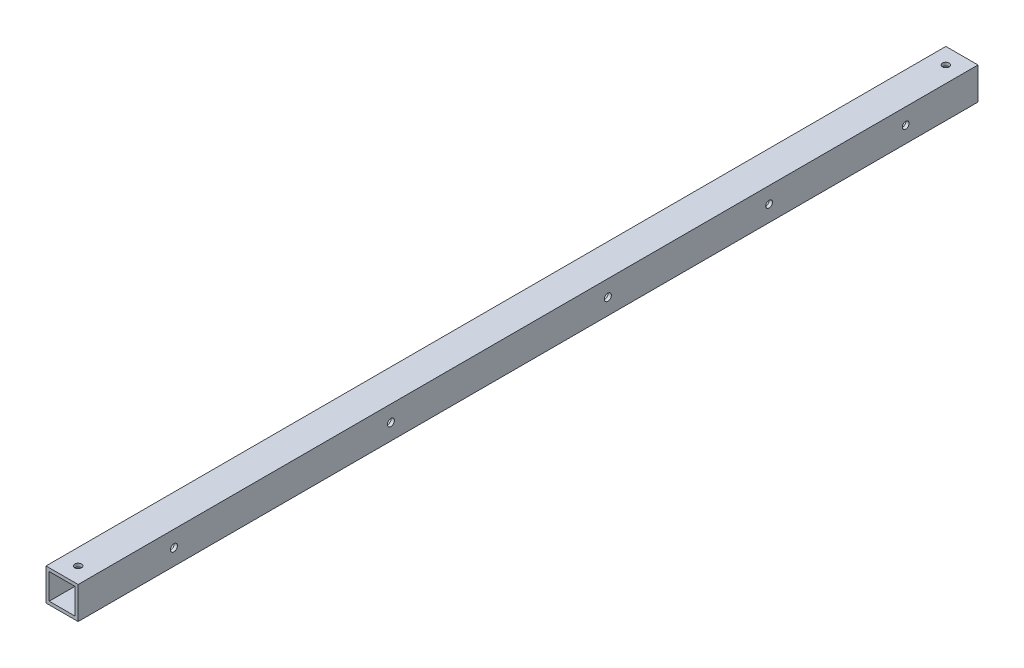
SolidWorks part; units mm, degrees
ref_plane "正面" through (0, 0, 0) normal (0, 0, 1) x (1, 0, 0)
ref_plane "平面" through (0, 0, 0) normal (0, 1, 0) x (1, 0, 0)
ref_plane "右側面" through (0, 0, 0) normal (1, 0, 0) x (0, 0, -1)
sketch "ｽｹｯﾁ1" plane through (0, 0, 0) normal (0, 0, 1) x (1, 0, 0)
  line L1 (-8, 8) -> (8, 8)
  line L2 (-8, 8) -> (-8, -8)
  line L3 (-8, -8) -> (8, -8)
  line L4 (8, 8) -> (8, -8)
  line L5 (-8, 8) -> (8, -8) construction
  line L6 (-8, -8) -> (8, 8) construction
  line L7 (-10, 10) -> (10, 10)
  line L8 (-10, 10) -> (-10, -10)
  line L9 (-10, -10) -> (10, -10)
  line L10 (10, 10) -> (10, -10)
  line L11 (-10, 10) -> (10, -10) construction
  line L12 (-10, -10) -> (10, 10) construction
  point P0 (0, 0)
  point P6 (0, 0)
  dimension "D1" = 20
  dimension "D2" = 20
  dimension "D3" = 16
  dimension "D4" = 16
extrude "ﾎﾞｽ - 押し出し1" add sketch "ｽｹｯﾁ1" along normal blind 560
sketch "ｽｹｯﾁ2" plane through (0, 10, 0) normal (0, 1, 0) x (1, 0, 0)
  line L0 (0, -560) -> (0, -550)
  line L1 (10, -560) -> (-10, -560) construction
  line L2 (0, 0) -> (0, -10)
  circle A0 centre (0, -550) radius 2.1
  circle A1 centre (0, -10) radius 2.1
  dimension "D2" = 4.2
  dimension "D4" = 4.2
  dimension "D1" = 10
  dimension "D3" = 10
extrude "ｶｯﾄ - 押し出し1" cut sketch "ｽｹｯﾁ2" against normal blind 10
sketch "ｽｹｯﾁ4" plane through (10, 0, 0) normal (1, 0, 0) x (0, 0, -1)
  line L0 (-560, 0) -> (-500.38, 0)
  line L1 (-560, -10) -> (-560, 10) construction
  line L2 (-500.38, 0) -> (-365.38, 0)
  line L3 (-365.38, 0) -> (-230.38, 0)
  circle A0 centre (-500.38, 0) radius 2.2
  circle A1 centre (-365.38, 0) radius 2.2
  circle A2 centre (-230.38, 0) radius 2.2
  dimension "D2" = 4.4
  dimension "D5" = 4.4
  dimension "D6" = 4.4
  dimension "D1" = 59.62
  dimension "D3" = 135
  dimension "D4" = 135
extrude "ｶｯﾄ - 押し出し3" cut sketch "ｽｹｯﾁ4" against normal through all
sketch "ｽｹｯﾁ5" plane through (10, 0, 0) normal (1, 0, 0) x (0, 0, -1)
  line L0 (0, 0) -> (-45, 0)
  line L1 (0, -10) -> (0, 10) construction
  line L2 (-45, 0) -> (-130, 0)
  circle A0 centre (-130, 0) radius 2.1
  circle A1 centre (-45, 0) radius 2.1
  dimension "D3" = 4.2
  dimension "D4" = 4.2
  dimension "D1" = 45
  dimension "D2" = 85
extrude "ｶｯﾄ - 押し出し4" cut sketch "ｽｹｯﾁ5" against normal blind 22
